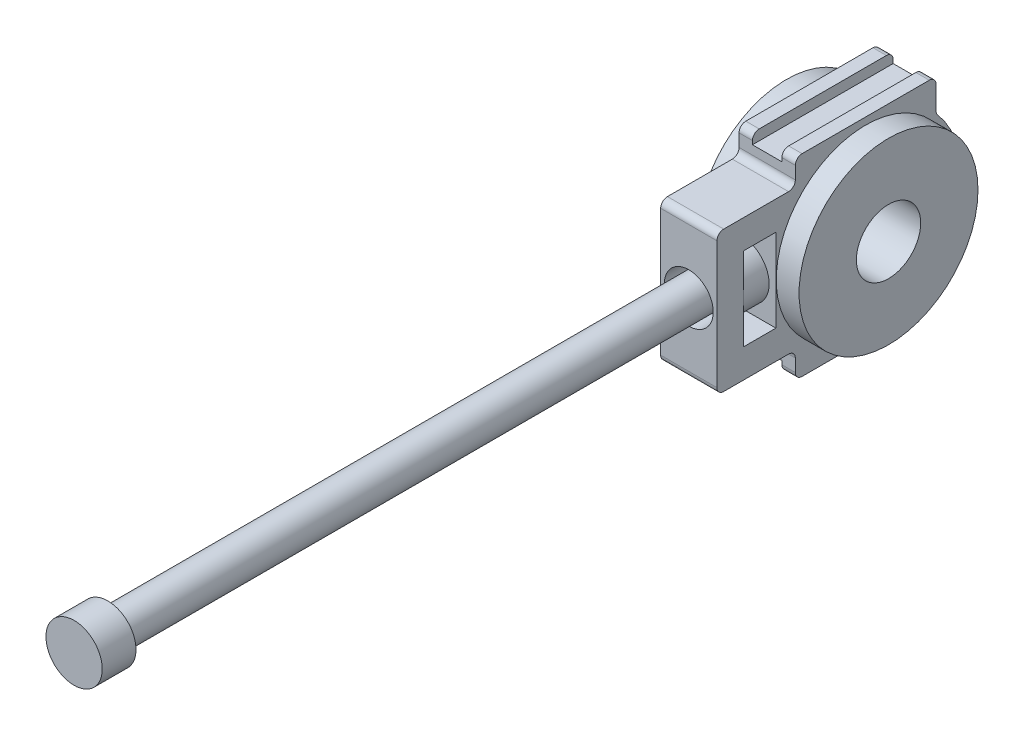
SolidWorks part; units mm, degrees
material "Plain Carbon Steel"
ref_plane "Front" through (0, 0, 0) normal (0, 0, 1) x (1, 0, 0)
ref_plane "Top" through (0, 0, 0) normal (0, 1, 0) x (1, 0, 0)
ref_plane "Right" through (0, 0, 0) normal (1, 0, 0) x (0, 0, -1)
sketch "Sketch1" plane through (0, 0, 0) normal (1, 0, 0) x (0, 0, -1)
  line L0 (-10.418, 14.2875) -> (10.418, -14.2875) construction
  line L1 (-10.418, 14.2875) -> (10.418, 14.2875)
  line L2 (-10.418, 14.2875) -> (-10.418, 10.418)
  line L3 (-10.418, -14.2875) -> (10.418, -14.2875)
  line L4 (10.418, 14.2875) -> (10.418, 9.4851)
  line L5 (0, 0) -> (-22.0266, 0) construction
  line L6 (-22.0266, 10.418) -> (-10.418, 10.418)
  line L7 (-22.0266, 10.418) -> (-22.0266, -10.418)
  line L8 (-22.0266, -10.418) -> (-10.418, -10.418)
  line L9 (-10.418, -10.418) -> (-10.418, -14.2875)
  line L10 (-10.418, 10.418) -> (-10.418, -10.418) construction
  line L11 (10.418, -9.4851) -> (10.418, -14.2875)
  line L12 (10.418, 9.4851) -> (10.418, -9.4851) construction
  arc A0 (10.418, -9.4851) -> (10.418, 9.4851) centre (0, 0) ccw
  arc A1 (10.418, 9.4851) -> (10.418, -9.4851) centre (0, 0) ccw construction
  dimension "D1" = 20.8359
  dimension "D6" = 14.0891
  dimension "D2" = 28.575
  dimension "D3" = 22.0266
  dimension "D4" = 20.8359
  dimension "D5" = 36.1156
extrude "Base-Extrude" add sketch "Sketch1" along normal mid plane 8.3344
sketch "Sketch2" plane through (0, 0, 0) normal (1, 0, 0) x (0, 0, -1)
  circle A0 centre (0, 0) radius 13.25
  dimension "D1" = 26.5
extrude "Boss-Extrude1" add sketch "Sketch2" along normal blind 7.55 and the other way blind 7.55
sketch "Sketch3" plane through (0, 0, 0) normal (1, 0, 0) x (0, 0, -1)
  line L0 (0, 0) -> (-18.0578, 0) construction
  line L1 (-18.0578, 6.1516) -> (-13.2953, 6.1516)
  line L2 (-18.0578, 6.1516) -> (-18.0578, -6.1516)
  line L3 (-18.0578, -6.1516) -> (-13.2953, -6.1516)
  line L4 (-13.2953, 6.1516) -> (-13.2953, -6.1516)
  line L5 (-22.0266, 10.418) -> (-22.0266, -10.418) construction
  circle A0 centre (0, 0) radius 4.7625
  dimension "D4" = 9.525
  dimension "D1" = 3.9688
  dimension "D2" = 4.7625
  dimension "D3" = 12.3031
extrude "Cut-Extrude1" cut sketch "Sketch3" against normal through all and the other way through all
sketch "Sketch4" plane through (0, 0, 22.0266) normal (0, 0, 1) x (1, 0, 0)
  circle A0 centre (0, 0) radius 3.175
  dimension "D1" = 6.35
extrude "Boss-Extrude3" add sketch "Sketch4" against normal up to surface (3.9688 mm away) up to face at (0, 0, 18.0578)
sketch "Sketch6" plane through (0, 0, 22.0266) normal (0, 0, 1) x (1, 0, 0)
  circle A0 centre (0, 0) radius 3.6215
  dimension "D1" = 7.243
extrude "Cut-Extrude2" cut sketch "Sketch6" against normal up to surface (3.9688 mm away) up to face at (0, 0, 18.0578)
fillet "Fillet1" radius 1 4 edges at (0, 9.4851, -10.418) (0, -9.4851, -10.418) (0, -10.418, 10.418) (0, 10.418, 10.418)
fillet "Fillet2" radius 1 6 edges at (0, -14.2875, -10.418) (0, 14.2875, -10.418) (0, -14.2875, 10.418) (0, -10.418, 22.0266) (0, 10.418, 22.0266) (0, 14.2875, 10.418)
sketch "Sketch7" plane through (0, 0, 0) normal (0, 0, 1) x (1, 0, 0)
  line L0 (4.1672, 14.2875) -> (-4.1672, 14.2875) construction
  line L1 (2.1828, 14.2875) -> (-2.1828, 14.2875)
  line L2 (4.1672, -14.2875) -> (-4.1672, -14.2875) construction
  line L3 (2.1828, -14.2875) -> (-2.1828, -14.2875)
  line L4 (-2.1828, 14.2875) -> (-2.1828, 12.7496)
  line L5 (-2.1828, 12.7496) -> (2.1828, 12.7496)
  line L6 (2.1828, 12.7496) -> (2.1828, 14.2875)
  line L7 (0, 12.7496) -> (0, -12.7496) construction
  line L8 (-2.1828, -12.7496) -> (2.1828, -12.7496)
  line L9 (-2.1828, -12.7496) -> (-2.1828, -14.2875)
  line L11 (2.1828, -12.7496) -> (2.1828, -14.2875)
  dimension "D1" = 4.3656
  dimension "D2" = 25.4992
extrude "Cut-Extrude3" cut sketch "Sketch7" against normal through all and the other way through all
sketch "Sketch8" plane through (0, 0, 13.2953) normal (0, 0, 1) x (1, 0, 0)
  circle A0 centre (0, 0) radius 4.1672
extrude "Boss-Extrude4" add sketch "Sketch8" along normal up to surface (3.7625 mm away) from offset 1 up to face at (3.6215, 0, 18.0578)
sketch "Sketch9" plane through (0, 0, 18.0578) normal (0, 0, 1) x (1, 0, 0)
  circle A0 centre (0, 0) radius 2.6215
  circle A1 centre (0, 0) radius 3.6215 construction
  dimension "D1" = 1
  dimension "D2" = 5.243
extrude "Boss-Extrude5" add sketch "Sketch9" along normal blind 90
sketch "Sketch10" plane through (0, 0, 108.0578) normal (0, 0, 1) x (1, 0, 0)
  circle A0 centre (0, 0) radius 4.1672
extrude "Boss-Extrude6" add sketch "Sketch10" along normal blind 5
